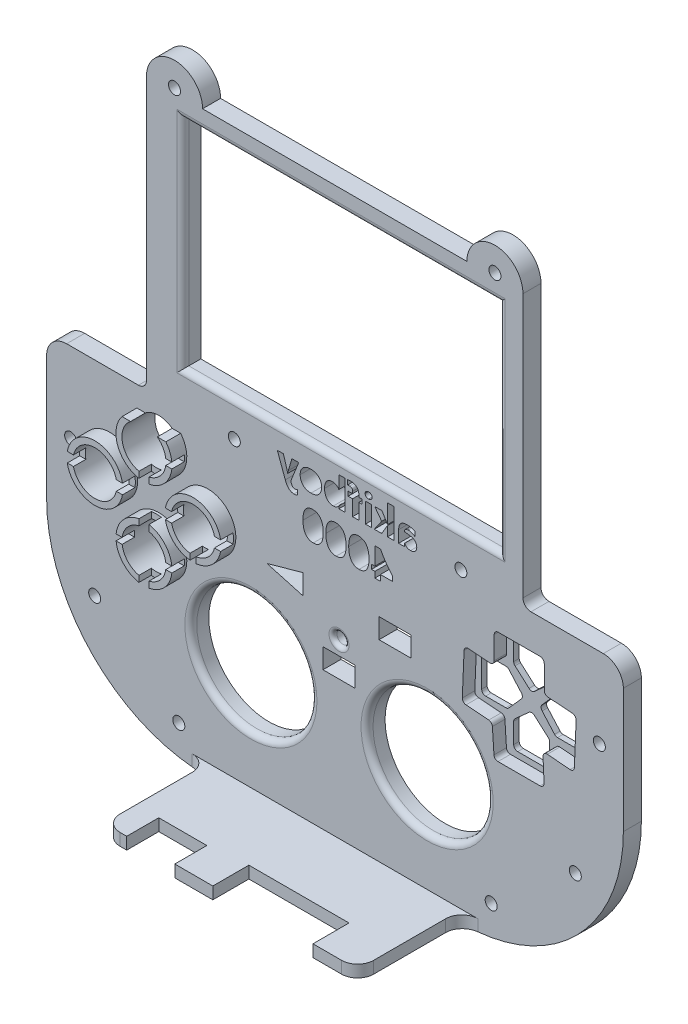
SolidWorks part; units mm, degrees
ref_plane "Front Plane" through (0, 0, 0) normal (0, 0, 1) x (1, 0, 0)
ref_plane "Top Plane" through (0, 0, 0) normal (0, 1, 0) x (1, 0, 0)
ref_plane "Right Plane" through (0, 0, 0) normal (1, 0, 0) x (0, 0, -1)
sketch "Sketch3" plane through (0, 0, 0) normal (0, 0, 1) x (1, 0, 0)
  line L1 (-43.07, -30) -> (43.07, -30)
  line L2 (-43.07, -30) -> (-43.07, 30)
  line L3 (-43.07, 30) -> (43.07, 30)
  line L4 (43.07, -30) -> (43.07, 30)
  line L5 (-43.07, -30) -> (43.07, 30) construction
  line L6 (-43.07, 30) -> (43.07, -30) construction
  line L7 (-47, -34) -> (47, -34)
  line L8 (-47, -34) -> (-47, 34)
  line L9 (-47, 34) -> (47, 34)
  line L10 (47, -34) -> (47, 34)
  line L11 (-47, -34) -> (47, 34) construction
  line L12 (-47, 34) -> (47, -34) construction
  line L13 (-71.93, -34) -> (72.07, -34)
  line L14 (-71.93, -34) -> (-71.93, -110)
  line L15 (-71.93, -110) -> (72.07, -110)
  line L16 (72.07, -34) -> (72.07, -110)
  line L17 (-67.93, -38) -> (68.07, -38)
  line L18 (-67.93, -38) -> (-67.93, -106)
  line L19 (-67.93, -106) -> (68.07, -106)
  line L20 (68.07, -38) -> (68.07, -106)
  point P0 (0, 0)
  point P6 (0, 0)
  dimension "D1" = 94
  dimension "D2" = 86.14
  dimension "D3" = 60
  dimension "D4" = 4
  dimension "D5" = 68
  dimension "D6" = 76
  dimension "D7" = 0
  dimension "D8" = 4
  dimension "D9" = 4
  dimension "D10" = 136
  dimension "D11" = 144
  dimension "D12" = 111.14
extrude "Boss-Extrude1" add sketch "Sketch3" along normal blind 4.5 contours L7 L10 L9 L8 L4 L1 L2 L3 | L16 L13 L7 L14 L15 L17 L20 L19 L18 | L1 L4 L3 L2 | L20 L17 L18 L19
fillet "Fillet1" radius 40 2 edges at (-71.93, -110, 2.25) (72.07, -110, 2.25)
fillet "Fillet3" radius 2 2 edges at (47, -34, 2.25) (-47, -34, 2.25)
fillet "Fillet4" radius 5 2 edges at (72.07, -34, 2.25) (-71.93, -34, 2.25)
sketch "Sketch7" plane through (0, 0, 4.5) normal (0, 0, 1) x (1, 0, 0)
  line L0 (-47, 34) -> (47, 34) construction
  line L1 (-43.07, 30) -> (43.07, 30)
  line L2 (-43.07, 30) -> (-43.07, -30)
  line L3 (-43.07, -30) -> (43.07, -30)
  line L4 (43.07, 30) -> (43.07, -30)
  line L5 (47, -32) -> (47, 34) construction
  circle A0 centre (-25.07, -33.7) radius 1.5
  circle A1 centre (31.5, -33.7) radius 1.5
  dimension "D5" = 3
  dimension "D6" = 3.7
  dimension "D8" = 3
  dimension "D9" = 3.7
  dimension "D10" = 15.5
  dimension "D7" = 18
  dimension "D1" = 60
  dimension "D2" = 4
  dimension "D3" = 86.14
  dimension "D4" = 3.93
extrude "Cut-Extrude1" cut sketch "Sketch7" against normal through all contours A1 | A0
sketch "Sketch8" plane through (0, 0, 4.5) normal (0, 0, 1) x (1, 0, 0)
  line L1 (-31.93, -110) -> (32.07, -110)
  line L2 (-31.93, -110) -> (-31.93, -107)
  line L3 (-31.93, -107) -> (32.07, -107)
  line L4 (32.07, -110) -> (32.07, -107)
  dimension "D1" = 64
  dimension "D2" = 3
extrude "Boss-Extrude2" add sketch "Sketch8" along normal blind 26
sketch "Sketch10" plane through (0, -110, 0) normal (0, -1, 0) x (1, 0, 0)
  line L0 (-31.93, 30.5) -> (32.07, 30.5) construction
  line L1 (-13.93, 22.5) -> (-25.93, 22.5)
  line L2 (-13.93, 22.5) -> (-13.93, 30.5)
  line L3 (-13.93, 30.5) -> (-25.93, 30.5)
  line L4 (-25.93, 22.5) -> (-25.93, 30.5)
  line L5 (-31.93, 30.5) -> (-31.93, 4.5) construction
  line L7 (20.57, 21.5) -> (-4.43, 21.5)
  line L8 (20.57, 21.5) -> (20.57, 30.5)
  line L9 (20.57, 30.5) -> (-4.43, 30.5)
  line L10 (-4.43, 21.5) -> (-4.43, 30.5)
  dimension "D1" = 8
  dimension "D2" = 12
  dimension "D3" = 0
  dimension "D4" = 6
  dimension "D5" = 9
  dimension "D6" = 25
  dimension "D7" = 0
  dimension "D8" = 9.5
extrude "Cut-Extrude2" cut sketch "Sketch10" against normal blind 4
sketch "Sketch12" plane through (0, 0, 0) normal (0, 0, -1) x (-1, 0, 0)
  line L0 (-47, -32) -> (-47, 34) construction
  line L1 (-41.07, 28.97) -> (37.93, 28.97)
  line L2 (-41.07, 28.97) -> (-41.07, -25.03)
  line L3 (-41.07, -25.03) -> (37.93, -25.03)
  line L4 (37.93, 28.97) -> (37.93, -25.03)
  line L5 (47, 34) -> (-47, 34) construction
  dimension "D1" = 79
  dimension "D2" = 54
  dimension "D3" = 5.93
  dimension "D4" = 5.03
extrude "Cut-Extrude3" cut sketch "Sketch12" against normal blind 4.5
sketch "Sketch13" plane through (0, 0, 0) normal (0, 0, -1) x (-1, 0, 0)
  line L0 (31.93, -110) -> (-32.07, -110) construction
  line L1 (71.93, -39) -> (71.93, -70) construction
  circle A0 centre (-23.07, -80) radius 15
  circle A1 centre (20.93, -80) radius 15
  dimension "D1" = 30
  dimension "D2" = 30
  dimension "D3" = 0
  dimension "D4" = 44
  dimension "D5" = 30
  dimension "D6" = 51
extrude "Cut-Extrude4" cut sketch "Sketch13" against normal blind 4.5
sketch "Sketch14" plane through (0, 0, 0) normal (0, 0, -1) x (-1, 0, 0)
  line L0 (-50.57, -50.5) -> (-46.07, -54.5)
  line L1 (-50.57, -44) -> (-41.57, -44)
  line L2 (-50.57, -44) -> (-50.57, -50.5)
  line L4 (-41.57, -44) -> (-41.57, -50.5)
  line L5 (-46.07, -54.5) -> (-41.57, -50.5)
  line L6 (-46.07, -44) -> (-46.07, -69) construction
  line L7 (-46.07, -56.5) -> (-58.57, -56.5) construction
  line L8 (-46.07, -56.5) -> (-33.57, -56.5) construction
  line L9 (-50.57, -69) -> (-50.57, -62.5)
  line L10 (-50.57, -69) -> (-41.57, -69)
  line L11 (-41.57, -69) -> (-41.57, -62.5)
  line L12 (-46.07, -58.5) -> (-41.57, -62.5)
  line L13 (-50.57, -62.5) -> (-46.07, -58.5)
  line L14 (-46.07, -56.5) -> (-35.2262, -67.3438) construction
  line L15 (-33.57, -52) -> (-33.57, -61)
  line L16 (-33.57, -61) -> (-40.07, -61)
  line L17 (-44.07, -56.5) -> (-40.07, -61)
  line L18 (-40.07, -52) -> (-44.07, -56.5)
  line L19 (-33.57, -52) -> (-40.07, -52)
  line L20 (-58.57, -52) -> (-52.07, -52)
  line L21 (-58.57, -52) -> (-58.57, -61)
  line L22 (-58.57, -61) -> (-52.07, -61)
  line L23 (-48.07, -56.5) -> (-52.07, -61)
  line L24 (-52.07, -52) -> (-48.07, -56.5)
  line L29 (-49, -34) -> (-67.07, -34) construction
  line L30 (-72.07, -39) -> (-72.07, -70) construction
  dimension "D1" = 9
  dimension "D2" = 6.5
  dimension "D3" = 10.5
  dimension "D4" = 4.5
  dimension "D5" = 25
  dimension "D6" = 12.5
  dimension "D7" = 12.5
  dimension "D9" = 10
  dimension "D10" = 13.5
extrude "Cut-Extrude5" cut sketch "Sketch14" against normal blind 4.5
fillet "Fillet7" radius 1 10 edges at (52.07, -61, 2.25) (48.07, -56.5, 2.25) (58.57, -61, 2.25) (58.57, -52, 2.25) (52.07, -52, 2.25) (50.57, -50.5, 2.25) (46.07, -54.5, 2.25) (41.57, -50.5, 2.25) (41.57, -44, 2.25) (50.57, -44, 2.25)
fillet "Fillet8" radius 1 10 edges at (40.07, -52, 2.25) (40.07, -61, 2.25) (50.57, -62.5, 2.25) (50.57, -69, 2.25) (41.57, -69, 2.25) (41.57, -62.5, 2.25) (46.07, -58.5, 2.25) (44.07, -56.5, 2.25) (33.57, -61, 2.25) (33.57, -52, 2.25)
sketch "Sketch15" plane through (0, 0, 4.5) normal (0, 0, 1) x (1, 0, 0)
  line L0 (42.57, -44) -> (49.57, -44) construction
  line L1 (39.82, -42.5) -> (52.32, -42.5)
  line L2 (39.82, -42.5) -> (39.82, -50.25)
  line L4 (52.32, -42.5) -> (52.32, -50.25)
  line L5 (50.57, -45) -> (50.57, -50.0509) construction
  line L6 (46.07, -42.5) -> (46.07, -70.5) construction
  line L7 (46.07, -56.5) -> (32.07, -56.5) construction
  line L8 (46.07, -56.5) -> (60.07, -56.5) construction
  line L10 (52.32, -70.5) -> (51.962, -62.6438)
  line L11 (39.82, -70.5) -> (52.32, -70.5)
  line L12 (39.82, -70.5) -> (39.32, -62.75)
  line L13 (46.07, -56.5) -> (57.7695, -68.6995) construction
  line L15 (31.8208, -62.159) -> (39.32, -62.75)
  line L16 (32.3437, -49.6699) -> (31.8208, -62.159)
  line L17 (32.3437, -49.6699) -> (39.82, -50.25)
  line L18 (60.3192, -50.841) -> (52.32, -50.25)
  line L19 (60.3192, -50.841) -> (59.7963, -63.3301)
  line L20 (59.7963, -63.3301) -> (51.962, -62.6438)
  dimension "D1" = 12.5
  dimension "D3" = 1.5
  dimension "D4" = 1.75
  dimension "D5" = 28
  dimension "D6" = 14
  dimension "D7" = 14
extrude "Cut-Extrude7" cut sketch "Sketch15" against normal blind 3.12
fillet "Fillet9" radius 1 12 edges at (31.8208, -62.159, 2.94) (39.32, -62.75, 2.94) (39.82, -70.5, 2.94) (52.32, -70.5, 2.94) (51.962, -62.6438, 2.94) (59.7963, -63.3301, 2.94) (60.3192, -50.841, 2.94) (52.32, -50.25, 2.94) (52.32, -42.5, 2.94) (39.82, -42.5, 2.94) (39.82, -50.25, 2.94) (32.3437, -49.6699, 2.94)
sketch "Sketch16" plane through (0, 0, 0) normal (0, 0, -1) x (-1, 0, 0)
  line L0 (43.93, -43.5) -> (43.93, -66) construction
  line L1 (43.93, -54.75) -> (31.68, -54.75) construction
  line L2 (43.93, -54.75) -> (56.18, -54.75) construction
  line L3 (66.93, -34) -> (49, -34) construction
  line L4 (71.93, -39) -> (71.93, -70) construction
  circle A0 centre (43.93, -43.5) radius 5.5
  circle A1 centre (31.68, -54.75) radius 5.5
  circle A2 centre (56.18, -54.75) radius 5.5
  circle A3 centre (43.93, -66) radius 5.5
  dimension "D1" = 11
  dimension "D5" = 11
  dimension "D6" = 11
  dimension "D7" = 11
  dimension "D8" = 9.5
  dimension "D9" = 15.75
  dimension "D2" = 22.5
  dimension "D3" = 12.25
  dimension "D4" = 12.25
extrude "Cut-Extrude8" cut sketch "Sketch16" against normal blind 8.2
sketch "Sketch17" plane through (0, 0, 4.5) normal (0, 0, 1) x (1, 0, 0)
  circle A0 centre (-43.93, -43.5) radius 7
  circle A1 centre (-31.68, -54.75) radius 7
  circle A2 centre (-43.93, -66) radius 7
  circle A3 centre (-56.18, -54.75) radius 7
  circle A4 centre (-56.18, -54.75) radius 5.1
  circle A5 centre (-43.93, -43.5) radius 5.1
  circle A6 centre (-31.68, -54.75) radius 5.1
  circle A7 centre (-43.93, -66) radius 5.1
  dimension "D1" = 14
  dimension "D2" = 14
  dimension "D3" = 14
  dimension "D4" = 14
extrude "Boss-Extrude3" add sketch "Sketch17" along normal blind 3.7
sketch "Sketch18" plane through (0, 0, 8.2) normal (0, 0, 1) x (1, 0, 0)
  line L0 (-61.28, -54.75) -> (-26.58, -54.75) construction
  line L1 (-43.93, -38.4) -> (-43.93, -71.1) construction
  line L2 (-61.28, -54.75) -> (-63.18, -54.75) construction
  line L3 (-43.93, -38.4) -> (-43.93, -36.5) construction
  line L4 (-26.58, -54.75) -> (-24.68, -54.75) construction
  line L5 (-43.93, -71.1) -> (-43.93, -73) construction
  line L6 (-56.18, -47.75) -> (-56.18, -61.75) construction
  line L7 (-63.6337, -53.5) -> (-61.0831, -53.5)
  line L8 (-63.6337, -53.5) -> (-63.6337, -56)
  line L9 (-63.6337, -56) -> (-61.0831, -56)
  line L10 (-61.0831, -53.5) -> (-61.0831, -56)
  line L11 (-48.7263, -56) -> (-51.2769, -56)
  line L12 (-51.2769, -53.5) -> (-51.2769, -56)
  line L13 (-48.7263, -53.5) -> (-51.2769, -53.5)
  line L14 (-48.7263, -53.5) -> (-48.7263, -56)
  line L15 (-50.93, -43.5) -> (-36.93, -43.5) construction
  line L16 (-45.18, -48.3135) -> (-42.68, -48.3135)
  line L17 (-45.18, -36.1634) -> (-42.68, -36.1634)
  line L18 (-45.18, -36.1634) -> (-45.18, -38.6865)
  line L19 (-45.18, -38.6865) -> (-42.68, -38.6865)
  line L20 (-42.68, -36.1634) -> (-42.68, -38.6865)
  line L21 (-42.68, -50.8366) -> (-42.68, -48.3135)
  line L22 (-45.18, -50.8366) -> (-42.68, -50.8366)
  line L23 (-45.18, -50.8366) -> (-45.18, -48.3135)
  line L24 (-31.68, -47.75) -> (-31.68, -61.75) construction
  line L25 (-36.3824, -42.75) -> (-39.3442, -42.75)
  line L26 (-36.3824, -42.75) -> (-36.3824, -44.25)
  line L27 (-36.3824, -44.25) -> (-39.3442, -44.25)
  line L28 (-39.3442, -42.75) -> (-39.3442, -44.25)
  line L29 (-50.93, -66) -> (-36.93, -66) construction
  line L30 (-38.8378, -53.5) -> (-36.5146, -53.5)
  line L31 (-38.8378, -53.5) -> (-38.8378, -56)
  line L32 (-38.8378, -56) -> (-36.5146, -56)
  line L33 (-36.5146, -53.5) -> (-36.5146, -56)
  line L34 (-27.0339, -53.5) -> (-24.6578, -53.5)
  line L35 (-27.0339, -53.5) -> (-27.0339, -56)
  line L36 (-27.0339, -56) -> (-24.6578, -56)
  line L37 (-24.6578, -53.5) -> (-24.6578, -56)
  line L38 (-32.43, -59.4866) -> (-30.93, -59.4866)
  line L39 (-32.43, -59.4866) -> (-32.43, -61.9161)
  line L40 (-32.43, -61.9161) -> (-30.93, -61.9161)
  line L41 (-30.93, -59.4866) -> (-30.93, -61.9161)
  line L42 (-45.18, -58.8863) -> (-42.68, -58.8863)
  line L43 (-45.18, -70.7123) -> (-42.68, -70.7123)
  line L44 (-45.18, -70.7123) -> (-45.18, -73.1137)
  line L45 (-45.18, -73.1137) -> (-42.68, -73.1137)
  line L46 (-42.68, -70.7123) -> (-42.68, -73.1137)
  line L47 (-42.68, -61.2877) -> (-42.68, -58.8863)
  line L48 (-45.18, -61.2877) -> (-42.68, -61.2877)
  line L49 (-45.18, -61.2877) -> (-45.18, -58.8863)
  line L50 (-36.8386, -66.75) -> (-39.642, -66.75)
  line L51 (-51.0214, -65.25) -> (-48.218, -65.25)
  line L52 (-51.0214, -65.25) -> (-51.0214, -66.75)
  line L53 (-51.0214, -66.75) -> (-48.218, -66.75)
  line L54 (-48.218, -65.25) -> (-48.218, -66.75)
  line L55 (-39.642, -65.25) -> (-39.642, -66.75)
  line L56 (-36.8386, -65.25) -> (-39.642, -65.25)
  line L57 (-36.8386, -65.25) -> (-36.8386, -66.75)
  circle A0 centre (-56.18, -54.75) radius 5.1 construction
  circle A1 centre (-31.68, -54.75) radius 5.1 construction
  circle A2 centre (-43.93, -43.5) radius 5.1 construction
  circle A3 centre (-43.93, -66) radius 5.1 construction
  circle A4 centre (-56.18, -54.75) radius 7 construction
  circle A5 centre (-56.18, -54.75) radius 7 construction
  circle A6 centre (-43.93, -43.5) radius 7 construction
  circle A7 centre (-31.68, -54.75) radius 7 construction
  circle A8 centre (-43.93, -66) radius 7 construction
  circle A9 centre (-43.93, -66) radius 7 construction
  circle A10 centre (-43.93, -43.5) radius 7 construction
  circle A11 centre (-31.68, -54.75) radius 7 construction
  point P50 (-43.93, -37.45)
  dimension "D1" = 2.5
  dimension "D2" = 1.25
  dimension "D3" = 2.5
  dimension "D4" = 1.25
  dimension "D5" = 1.5
  dimension "D6" = 0.75
  dimension "D7" = 2.5
  dimension "D8" = 1.25
  dimension "D9" = 2.5
  dimension "D10" = 1.25
  dimension "D11" = 1.5
  dimension "D12" = 0.75
  dimension "D13" = 2.5
  dimension "D14" = 1.25
  dimension "D15" = 1.5
  dimension "D16" = 2.8034
  dimension "D17" = 0.75
extrude "Cut-Extrude9" cut sketch "Sketch18" against normal blind 3.1
sketch "Sketch19" plane through (0, 0, 0) normal (0, 0, -1) x (-1, 0, 0)
  line L0 (7.93, -54) -> (7.93, -59)
  line L1 (-19.07, -54) -> (-11.07, -54)
  line L2 (-19.07, -54) -> (-19.07, -59)
  line L3 (-19.07, -59) -> (-11.07, -59)
  line L4 (-11.07, -54) -> (-11.07, -59)
  line L5 (-5.07, -67.5) -> (2.93, -67.5)
  line L6 (-5.07, -67.5) -> (-5.07, -72.5)
  line L7 (-5.07, -72.5) -> (2.93, -72.5)
  line L8 (2.93, -67.5) -> (2.93, -72.5)
  line L9 (7.93, -59) -> (16.93, -56.5)
  line L10 (16.93, -56.5) -> (7.93, -54)
  line L11 (-72.07, -39) -> (-72.07, -70) construction
  line L12 (-49, -34) -> (-67.07, -34) construction
  circle A0 centre (-1.07, -64) radius 1.5
  point P11 (7.93, -56.5)
  dimension "D13" = 3
  dimension "D14" = 3.5
  dimension "D15" = 4
  dimension "D1" = 8
  dimension "D2" = 5
  dimension "D3" = 8
  dimension "D4" = 5
  dimension "D5" = 5
  dimension "D6" = 9
  dimension "D7" = 2.5
  dimension "D8" = 19
  dimension "D9" = 6
  dimension "D10" = 53
  dimension "D11" = 20
  dimension "D12" = 8.5
extrude "Cut-Extrude10" cut sketch "Sketch19" against normal blind 4.5
sketch "Sketch20" plane through (0, 34, 0) normal (0, 1, 0) x (1, 0, 0)
  line L1 (-47, 0) -> (47, 0)
  line L2 (-47, 0) -> (-47, -4.5)
  line L3 (-47, -4.5) -> (47, -4.5)
  line L4 (47, 0) -> (47, -4.5)
extrude "Cut-Extrude11" cut sketch "Sketch20" against normal blind 0.23
sketch "Sketch21" plane through (0, 0, 0) normal (0, 0, -1) x (-1, 0, 0)
  line L0 (31.93, -110) -> (-32.07, -110) construction
  line L1 (-72.07, -39) -> (-72.07, -70) construction
  line L2 (-0.07, -110) -> (-0.07, -83.0684) construction
  circle A0 centre (-39.07, -102) radius 1.5
  circle A1 centre (38.93, -102) radius 1.5
  dimension "D1" = 3
  dimension "D2" = 8
  dimension "D3" = 33
extrude "Cut-Extrude12" cut sketch "Sketch21" against normal blind 4.5
sketch "Sketch22" plane through (0, 0, 0) normal (0, 0, -1) x (-1, 0, 0)
  line L0 (-47, 33.77) -> (47, 33.77) construction
  line L1 (-47, 33.77) -> (-33, 33.77)
  line L2 (0, 33.77) -> (0, 51.7218) construction
  line L3 (47, 33.77) -> (33, 33.77)
  arc A0 (-47, 33.77) -> (-33, 33.77) centre (-40, 33.77) cw
  arc A1 (47, 33.77) -> (33, 33.77) centre (40, 33.77) ccw
  dimension "D1" = 7
extrude "Boss-Extrude4" add sketch "Sketch22" against normal blind 4.5
sketch "Sketch23" plane through (0, 0, 0) normal (0, 0, -1) x (-1, 0, 0)
  line L0 (0, 33.77) -> (0, 51.0593) construction
  line L1 (-33, 33.77) -> (33, 33.77) construction
  line L2 (-47, 33.77) -> (47, 33.77) construction
  line L3 (40, 33.77) -> (40, 40.77) construction
  line L4 (-40, 33.77) -> (-40, 40.77) construction
  arc A0 (47, 33.77) -> (33, 33.77) centre (40, 33.77) ccw construction
  arc A1 (-33, 33.77) -> (-47, 33.77) centre (-40, 33.77) ccw construction
  circle A2 centre (-40, 34.77) radius 1.5
  circle A3 centre (40, 34.77) radius 1.5
  dimension "D1" = 3
  dimension "D2" = 1
extrude "Cut-Extrude13" cut sketch "Sketch23" against normal blind 4.5
sketch "Sketch24" plane through (0, 0, 0) normal (0, 0, -1) x (-1, 0, 0)
  line L0 (-0.07, -110) -> (-0.07, -87.0566) construction
  line L1 (31.93, -110) -> (-32.07, -110) construction
  line L2 (66.93, -34) -> (49, -34) construction
  line L3 (71.93, -39) -> (71.93, -70) construction
  circle A0 centre (65.93, -54) radius 1.5
  circle A1 centre (59.93, -85) radius 1.5
  circle A2 centre (-66.07, -54) radius 1.5
  circle A3 centre (-60.07, -85) radius 1.5
  dimension "D1" = 3
  dimension "D2" = 3
  dimension "D3" = 20
  dimension "D4" = 6
  dimension "D5" = 12
  dimension "D6" = 51
extrude "Cut-Extrude14" cut sketch "Sketch24" against normal blind 4.5
sketch "Sketch25" plane through (0, 0, 0) normal (0, 0, -1) x (-1, 0, 0)
  line L0 (-31.5, -33.7) -> (-31.5, -35.7) construction
  line L1 (25.07, -33.7) -> (25.07, -35.7) construction
  line L2 (25.07, -35.7) -> (-31.5, -35.7) construction
  line L3 (-31.5, -46.2) -> (25.07, -46.2) construction
  text T0 "akifboy" font "Segoe UI" height 7
  text T1 "4000" font "Segoe UI" height 7
  dimension "D1" = 2
  dimension "D2" = 10.5
extrude "Cut-Extrude20" cut sketch "Sketch25" against normal blind 4.5
sketch "Sketch26" plane through (0, 0, 4.5) normal (0, 0, -1) x (-1, 0, 0)
  circle A0 centre (43.93, -66) radius 5.5
  circle A1 centre (56.18, -54.75) radius 5.5
  circle A2 centre (43.93, -43.5) radius 5.5
  circle A3 centre (31.68, -54.75) radius 5.5
extrude "Cut-Extrude21" cut sketch "Sketch26" against normal blind 10
sketch "Sketch27" plane through (0, 0, 8.2) normal (0, 0, 1) x (1, 0, 0)
  line L1 (-50.2378, -35.5122) -> (-37.0757, -35.5122)
  line L2 (-50.2378, -35.5122) -> (-50.2378, -39.1291)
  line L3 (-50.2378, -39.1291) -> (-37.0757, -39.1291)
  line L4 (-37.0757, -35.5122) -> (-37.0757, -39.1291)
extrude "Cut-Extrude22" cut sketch "Sketch27" against normal blind 3.7
fillet "Fillet12" radius 1.5 6 edges at (-35.93, -80, 4.5) (8.07, -80, 4.5) (-37.93, 1.97, 4.5) (1.57, -25.03, 4.5) (41.07, 1.97, 4.5) (1.57, 28.97, 4.5)
fillet "Fillet13" radius 1 1 edges at (-0.43, -64, 4.5)
sketch "Sketch28" plane through (32.07, 0, 0) normal (1, 0, 0) x (0, 0, -1)
  line L1 (-34.0562, -103.8417) -> (-4.5, -103.8417)
  line L2 (-34.0562, -103.8417) -> (-34.0562, -110)
  line L3 (-34.0562, -110) -> (-4.5, -110)
  line L4 (-4.5, -103.8417) -> (-4.5, -110)
extrude "Cut-Extrude23" cut sketch "Sketch28" against normal blind 0.35
sketch "Sketch29" plane through (-31.93, 0, 0) normal (-1, 0, 0) x (0, 0, 1)
  line L1 (31.597, -105.009) -> (4.5, -105.009)
  line L2 (31.597, -105.009) -> (31.597, -110)
  line L3 (31.597, -110) -> (4.5, -110)
  line L4 (4.5, -105.009) -> (4.5, -110)
extrude "Cut-Extrude24" cut sketch "Sketch29" against normal blind 0.35
fillet "Fillet14" radius 4 4 edges at (31.72, -108.5, 4.5) (31.72, -108.5, 30.5) (-31.58, -108.5, 30.5) (-31.58, -108.5, 4.5)
